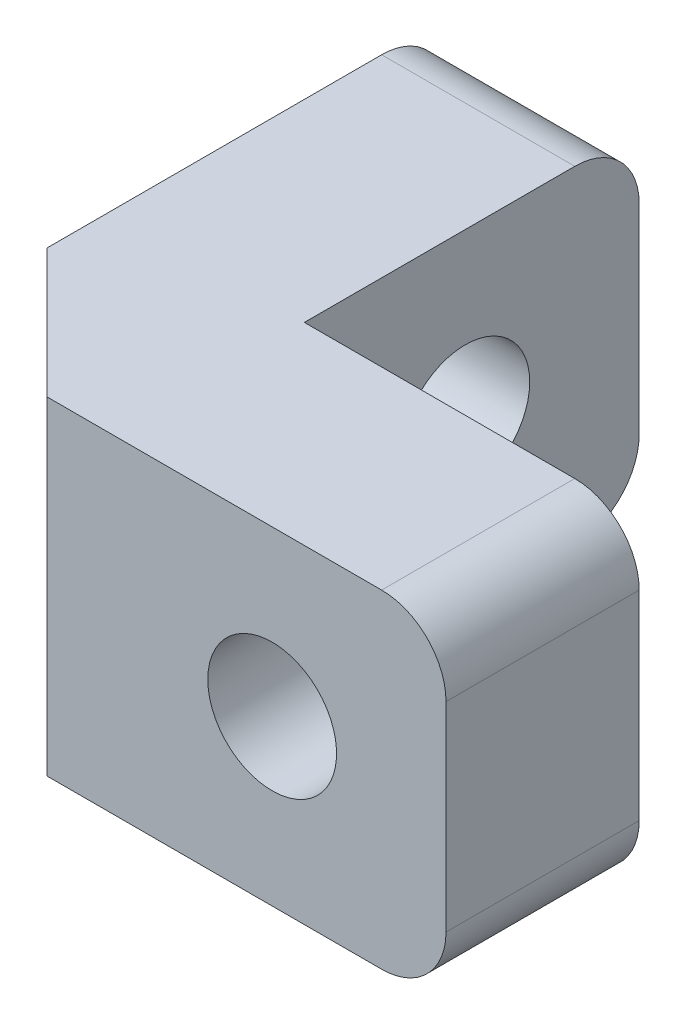
SolidWorks part; units mm, degrees
material "Custom Plastic"
ref_plane "Front Plane" through (0, 0, 0) normal (0, 0, 1) x (1, 0, 0)
ref_plane "Top Plane" through (0, 0, 0) normal (0, 1, 0) x (1, 0, 0)
ref_plane "Right Plane" through (0, 0, 0) normal (1, 0, 0) x (0, 0, -1)
sketch "Sketch1" plane through (0, 0, 0) normal (0, 1, 0) x (1, 0, 0)
  line L0 (0, 0) -> (0, 5.2)
  line L1 (0, 5.2) -> (-3, 5.2)
  line L2 (-3, 5.2) -> (-3, -3)
  line L3 (-3, -3) -> (5.2, -3)
  line L4 (5.2, -3) -> (5.2, 0)
  line L5 (0, 0) -> (5.2, 0)
  dimension "D1" = 5.2
  dimension "D2" = 3
  dimension "D3" = 8.2
  dimension "D4" = 8.2
  dimension "D5" = 3
extrude "Boss-Extrude1" add sketch "Sketch1" along normal blind 5.1
chamfer "Chamfer1" distance 2 angle 45 1 edges at (-3, 2.55, 3)
fillet "Fillet1" radius 1 4 edges at (5.2, 0, 1.5) (5.2, 5.1, 1.5) (-1.5, 0, -5.2) (-1.5, 5.1, -5.2)
sketch "Sketch3" plane through (0, 0, 0) normal (1, 0, 0) x (0, 0, -1)
  line L1 (0, 5.1) -> (4.2, 5.1) construction
  line L2 (0, 5.1) -> (0, 0) construction
  circle A0 centre (2.5, 2.55) radius 1
  point P0 (2.5, 2.55)
  dimension "D3" = 2
  dimension "D1" = 2.5
  dimension "D2" = 2.55
extrude "Cut-Extrude1" cut sketch "Sketch3" against normal blind 5.1
sketch "Sketch4" plane through (0, 0, 0) normal (0, 0, -1) x (-1, 0, 0)
  line L0 (-4.2, 0) -> (0, 0) construction
  line L1 (0, 5.1) -> (0, 0) construction
  circle A0 centre (-2.5, 2.55) radius 1
  point P0 (-2.5, 2.55)
  dimension "D3" = 2
  dimension "D1" = 2.55
  dimension "D2" = 2.5
extrude "Cut-Extrude2" cut sketch "Sketch4" against normal blind 5.1
sketch "Sketch5" plane through (0, 0, 0) normal (0, 0, -1) x (-1, 0, 0)
  circle A0 centre (-2.5, 2.55) radius 1.7
  dimension "D1" = 3.4
extrude "Cut-Extrude3" cut sketch "Sketch5" against normal blind 1.4
sketch "Sketch6" plane through (-3, 0, 0) normal (-1, 0, 0) x (0, 0, 1)
  circle A0 centre (-2.5, 2.55) radius 1.7
  dimension "D1" = 3.4
extrude "Cut-Extrude4" cut sketch "Sketch6" against normal blind 1.4
